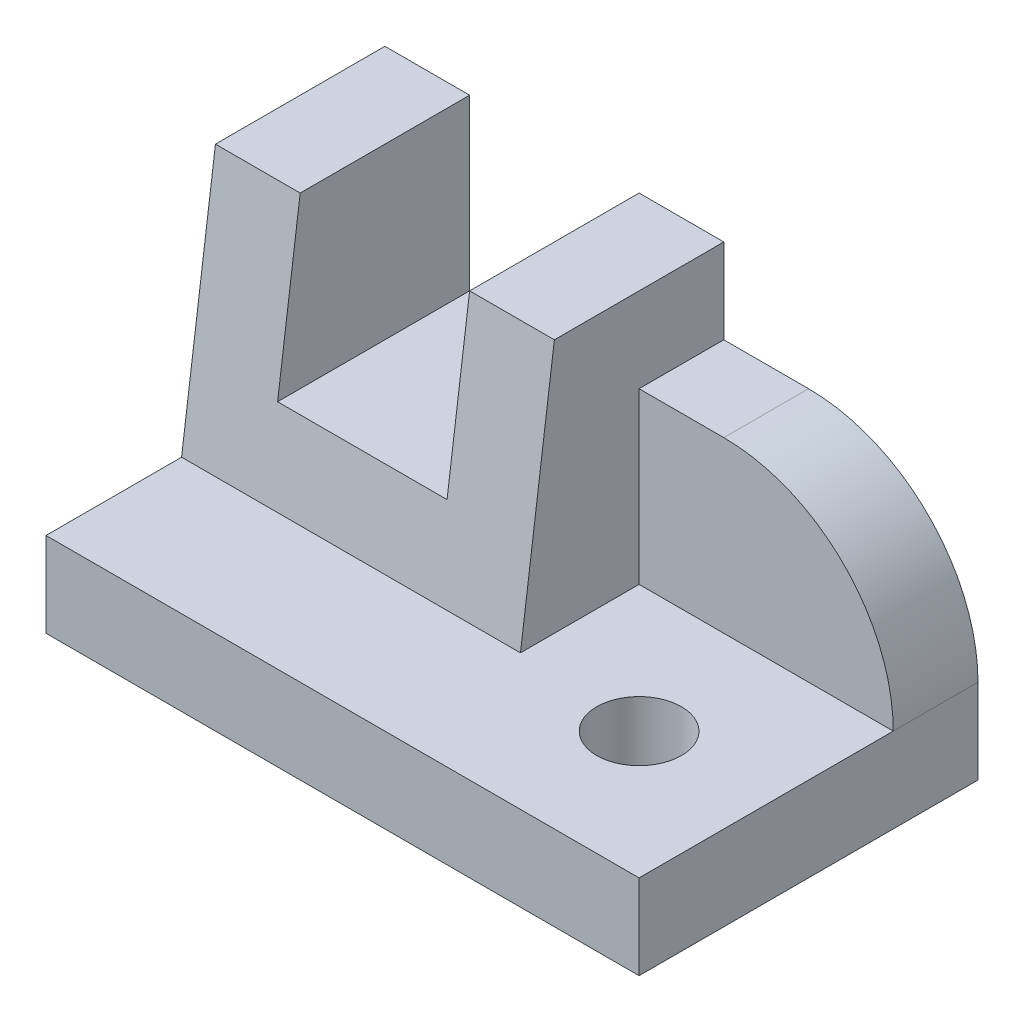
SolidWorks part; units mm, degrees
ref_plane "Front Plane" through (0, 0, 0) normal (0, 0, 1) x (1, 0, 0)
ref_plane "Top Plane" through (0, 0, 0) normal (0, 1, 0) x (1, 0, 0)
ref_plane "Right Plane" through (0, 0, 0) normal (1, 0, 0) x (0, 0, -1)
ref_plane "Plane1" through (0, 0, 0) normal (-1, 0, 0) x (0, -1, 0)
sketch "Sketch1" plane through (0, 0, 0) normal (-1, 0, 0) x (0, -1, 0)
  line L0 (-10, -16) -> (-40, -20)
  line L1 (-40, -20) -> (-10, -20)
  line L2 (-10, -20) -> (-10, -16)
  dimension "D1" = 30
  dimension "Width" = 4
extrude "Boss-Extrude1" add sketch "Sketch1" against normal blind 40
sketch "Sketch2" plane through (0, 0, -20) normal (0, 0, -1) x (-1, 0, 0)
  line L0 (-40, 40) -> (0, 40)
  line L1 (0, 40) -> (0, 10)
  line L2 (0, 10) -> (-40, 10)
  line L3 (-40, 10) -> (-40, 40)
extrude "Boss-Extrude2" add sketch "Sketch2" along normal blind 20
sketch "Sketch3" plane through (40, 0, 0) normal (1, 0, 0) x (0, 0, -1)
  line L0 (40, 10) -> (0, 10)
  line L1 (0, 10) -> (20, 40)
  line L2 (20, 40) -> (40, 40)
  line L3 (40, 40) -> (40, 10)
extrude "Boss-Extrude3" add sketch "Sketch3" along normal blind 30
sketch "Sketch4" plane through (70, 0, 0) normal (1, 0, 0) x (0, 0, -1)
  line L0 (20, 40) -> (0, 10)
  line L1 (0, 10) -> (30, 10)
  line L2 (30, 10) -> (30, 30)
  line L3 (30, 30) -> (40, 30)
  line L4 (40, 30) -> (40, 40)
  line L5 (40, 40) -> (20, 40)
extrude "Cut-Extrude1" cut sketch "Sketch4" against normal blind 30
sketch "Sketch5" plane through (0, 10, 0) normal (0, -1, 0) x (1, 0, 0)
  line L0 (70, 0) -> (70, -40)
  line L1 (70, -40) -> (0, -40)
  line L2 (0, -40) -> (0, 0)
  line L3 (0, 0) -> (70, 0)
extrude "Boss-Extrude4" add sketch "Sketch5" along normal blind 10
sketch "Sketch6" plane through (0, 0, -40) normal (0, 0, -1) x (-1, 0, 0)
  line L0 (-30, 40) -> (-30, 20)
  line L1 (-30, 20) -> (-10, 20)
  line L2 (-10, 20) -> (-10, 40)
  line L3 (-10, 40) -> (-30, 40)
extrude "Cut-Extrude2" cut sketch "Sketch6" against normal through all
hole_wizard "Ø10.0 (10) Diameter Hole1" positions "Sketch8" profile "Sketch7" hole size "Ø10.0" standard "ANSI Metric"
sketch "Sketch8" plane through (0, 0, 0) normal (0, -1, 0) x (-1, 0, 0)
  point P0 (-55, 15)
sketch "Sketch7" plane through (55, 0, -15) normal (1, 0, 0) x (0, 0, -1)
  line L0 (0, 0) -> (0, 40)
  line L1 (0, 40) -> (5, 40)
  line L2 (5, 40) -> (5, 0)
  line L5 (5, 0) -> (0, 0)
  line L11 (0, -6.35) -> (0, 107.95) construction
  dimension "Thru Hole Dia." = 10
  dimension "Thru Hole Depth" = 40
fillet "Fillet1" radius 20 1 edges at (70, 30, -35)
